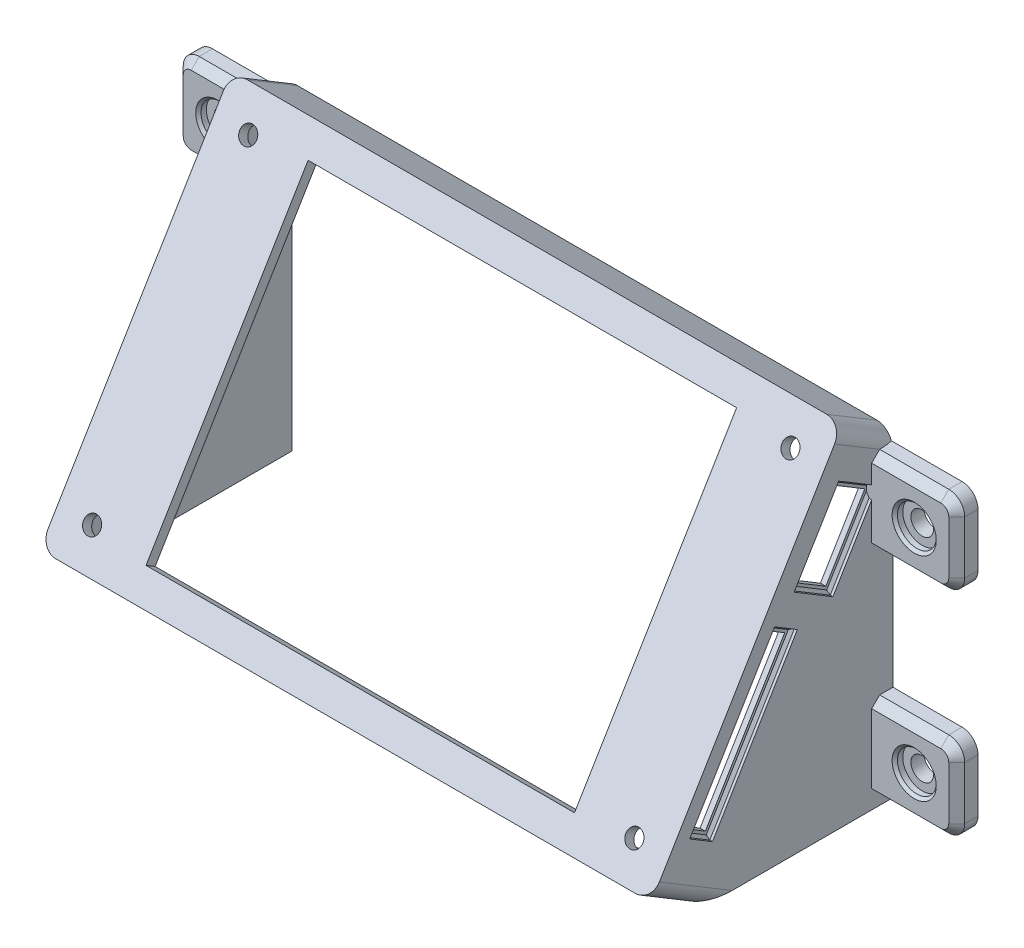
SolidWorks part; units mm, degrees
ref_plane "Front Plane" through (0, 0, 0) normal (0, 0, 1) x (1, 0, 0)
ref_plane "Top Plane" through (0, 0, 0) normal (0, 1, 0) x (1, 0, 0)
ref_plane "Right Plane" through (0, 0, 0) normal (1, 0, 0) x (0, 0, -1)
sketch "Sketch1" plane through (0, 0, 0) normal (1, 0, 0) x (0, 0, -1)
  line L0 (0, 0) -> (0, 60)
  line L1 (0, 60) -> (-36.0555, 0)
  line L2 (-36.0555, 0) -> (0, 0)
  dimension "D1" = 60
  dimension "D2" = 70
extrude "Boss-Extrude1" add sketch "Sketch1" along normal blind 115
sketch "Sketch2" plane through (0, 15.9184, 26.4898) normal (0, 0.5151, 0.8571) x (1, 0, 0)
  line L1 (0, 51.4286) -> (115, 51.4286)
  line L2 (0, 51.4286) -> (0, -18.5714)
  line L3 (0, -18.5714) -> (115, -18.5714)
  line L4 (115, 51.4286) -> (115, -18.5714)
extrude "Boss-Extrude2" add sketch "Sketch2" along normal blind 11
fillet "Fillet1" radius 3 4 edges at (0, 2.8329, 40.7698) (0, 62.8329, 4.7143) (115, 2.8329, 40.7698) (115, 62.8329, 4.7143)
shell "Shell1" thickness 2
sketch "Sketch3" plane through (0, 21.5842, 35.9183) normal (0, 0.5151, 0.8571) x (1, 0, 0)
  line L0 (0, 48.4286) -> (0, -15.5714) construction
  line L1 (112, 51.4286) -> (3, 51.4286) construction
  line L2 (115, -15.5714) -> (115, 48.4286) construction
  line L3 (3, -18.5714) -> (112, -18.5714) construction
  circle A0 centre (6.5, 44.9286) radius 1.6
  circle A1 centre (6.5, -12.0714) radius 1.6
  circle A2 centre (108.5, -12.0714) radius 1.6
  circle A3 centre (108.5, 44.9286) radius 1.6
  dimension "D1" = 3.2
  dimension "D2" = 6.5
  dimension "D3" = 6.5
  dimension "D4" = 6.5
  dimension "D5" = 6.5
extrude "Cut-Extrude1" cut sketch "Sketch3" against normal up to surface (2 mm away) up to face at (57.5, 34.6357, 25.742)
sketch "Sketch4" plane through (0, 21.5842, 35.9183) normal (0, 0.5151, 0.8571) x (1, 0, 0)
  line L0 (112, 51.4286) -> (3, 51.4286) construction
  line L1 (17.2, 46.0286) -> (97.8, 46.0286)
  line L2 (17.2, 46.0286) -> (17.2, -13.1714)
  line L3 (17.2, -13.1714) -> (97.8, -13.1714)
  line L4 (97.8, 46.0286) -> (97.8, -13.1714)
  line L5 (0, 48.4286) -> (0, -15.5714) construction
  dimension "D1" = 59.2
  dimension "D2" = 80.6
  dimension "D3" = 5.4
  dimension "D4" = 17.2
extrude "Cut-Extrude2" cut sketch "Sketch4" against normal up to surface (2 mm away) up to face at (108.5, 57.6929, 11.8864)
sketch "Sketch5" plane through (115, 0, 0) normal (1, 0, 0) x (0, 0, -1)
  line L0 (-36.8615, 12.7343) -> (-34.29, 11.1891)
  line L1 (-34.29, 11.1891) -> (-19.3528, 36.0462)
  line L2 (-19.3528, 36.0462) -> (-21.9242, 37.5915)
  line L3 (-21.9242, 37.5915) -> (-36.8615, 12.7343)
  line L4 (-43.9388, 8.2373) -> (-10.9738, 63.0944) construction
  line L5 (-36.0555, 0) -> (-45.4841, 5.6659) construction
  line L6 (-17.2077, 43.1105) -> (-9.8729, 55.3162)
  line L7 (-9.8729, 55.3162) -> (-4.3015, 51.9682)
  line L8 (-4.3015, 51.9682) -> (-11.6362, 39.7625)
  line L9 (-11.6362, 39.7625) -> (-17.2077, 43.1105)
  line L10 (0, 56.5) -> (-10.9738, 63.0944) construction
  line L11 (-9.4286, 65.6659) -> (0, 60) construction
  dimension "D1" = 3
  dimension "D2" = 29
  dimension "D3" = 10.5
  dimension "D4" = 3.75
  dimension "D5" = 9.1
  dimension "D6" = 4.95
  dimension "D7" = 6.5
  dimension "D8" = 14.24
extrude "Cut-Extrude3" cut sketch "Sketch5" against normal up to surface (2 mm away) up to face at (113, 25.1543, 16.343)
sketch "Sketch6" plane through (115, 0, 0) normal (1, 0, 0) x (0, 0, -1)
  line L8 (-38.2337, 12.3923) -> (-33.948, 9.8169)
  line L9 (-33.948, 9.8169) -> (-17.9805, 36.3883)
  line L10 (-17.9805, 36.3883) -> (-22.2663, 38.9637)
  line L11 (-22.2663, 38.9637) -> (-38.2337, 12.3923)
  line L12 (-38.2337, 12.3923) -> (-33.948, 9.8169)
  line L13 (-33.948, 9.8169) -> (-17.9805, 36.3883)
  line L14 (-17.9805, 36.3883) -> (-22.2663, 38.9637)
  line L15 (-22.2663, 38.9637) -> (-38.2337, 12.3923)
  line L20 (-11.2942, 38.3903) -> (-2.9293, 52.3103)
  line L21 (-2.9293, 52.3103) -> (-10.215, 56.6884)
  line L22 (-10.215, 56.6884) -> (-18.5799, 42.7684)
  line L23 (-18.5799, 42.7684) -> (-11.2942, 38.3903)
  line L24 (-11.2942, 38.3903) -> (-2.9293, 52.3103)
  line L25 (-2.9293, 52.3103) -> (-10.215, 56.6884)
  line L26 (-10.215, 56.6884) -> (-18.5799, 42.7684)
  line L27 (-18.5799, 42.7684) -> (-11.2942, 38.3903)
  dimension "D1" = 1
  dimension "D2" = 1
extrude "Cut-Extrude4" cut sketch "Sketch6" against normal blind 1
ref_plane "Plane1" through (57.5, 0, 0) normal (1, 0, 0) x (0, 0, -1)
chamfer "Chamfer3" distance 0.5 angle 45 8 edges at (114, 37.676, 20.1234) (114, 23.1026, 25.9643) (114, 25.678, 30.25) (114, 11.1046, 36.0908) (114, 40.5794, 14.937) (114, 49.7284, 14.3974) (114, 54.4994, 6.5721) (114, 45.3503, 7.1117)
sketch "Sketch7" plane through (115, 0, 0) normal (1, 0, 0) x (0, 0, -1)
  line L0 (0, 0) -> (0, 56.5) construction
  line L1 (0, 58) -> (-4, 58)
  line L2 (0, 58) -> (0, 42)
  line L3 (0, 42) -> (-4, 42)
  line L4 (-4, 58) -> (-4, 42)
  line L5 (-30.2312, 0) -> (0, 0) construction
  line L6 (0, 18) -> (-4, 18)
  line L7 (0, 18) -> (0, 2)
  line L8 (0, 2) -> (-4, 2)
  line L9 (-4, 18) -> (-4, 2)
  dimension "D1" = 16
  dimension "D2" = 2
  dimension "D3" = 24
  dimension "D4" = 4
extrude "Boss-Extrude3" add sketch "Sketch7" along normal blind 16 and the other way blind 2
sketch "Sketch8" plane through (0, 0, 4) normal (0, 0, 1) x (1, 0, 0)
  line L0 (123, 58) -> (123, 42) construction
  line L1 (115, 58) -> (131, 58) construction
  line L2 (115, 42) -> (131, 42) construction
  line L3 (123, 18) -> (123, 2) construction
  line L4 (115, 18) -> (131, 18) construction
  line L5 (115, 2) -> (131, 2) construction
  circle A0 centre (123, 50) radius 2.125
  circle A1 centre (123, 10) radius 2.125
  dimension "D1" = 4.25
extrude "Cut-Extrude5" cut sketch "Sketch8" against normal blind 4
sketch "Sketch9" plane through (0, 0, 4) normal (0, 0, 1) x (1, 0, 0)
  circle A0 centre (123, 50) radius 3.65
  circle A1 centre (123, 10) radius 3.65
  dimension "D1" = 7.3
extrude "Cut-Extrude6" cut sketch "Sketch9" against normal blind 1.5
chamfer "Chamfer4" distance 0.5 angle 45 2 edges at (126.65, 10, 4) (126.65, 50, 4)
fillet "Fillet2" radius 3 4 edges at (131, 18, 2) (131, 2, 2) (131, 58, 2) (131, 42, 2)
mirror "Mirror1" about plane through (57.5, 0, 0) normal (1, 0, 0) of "Fillet2", "Chamfer4", "Cut-Extrude6", "Cut-Extrude5", "Boss-Extrude3"
chamfer "Chamfer5" distance 1.5 angle 45 20 edges at (-6.5, 58, 4) (-15.1213, 57.1213, 4) (-16, 50, 4) (-15.1213, 42.8787, 4) (-6.5, 42, 4) (-6.5, 18, 4) (-15.1213, 17.1213, 4) (-16, 10, 4) (-15.1213, 2.8787, 4) (-6.5, 2, 4) (121.5, 2, 4) (130.1213, 2.8787, 4) (131, 10, 4) (130.1213, 17.1213, 4) (121.5, 18, 4) (121.5, 42, 4) (130.1213, 42.8787, 4) (131, 50, 4) (130.1213, 57.1213, 4) (121.5, 58, 4)
